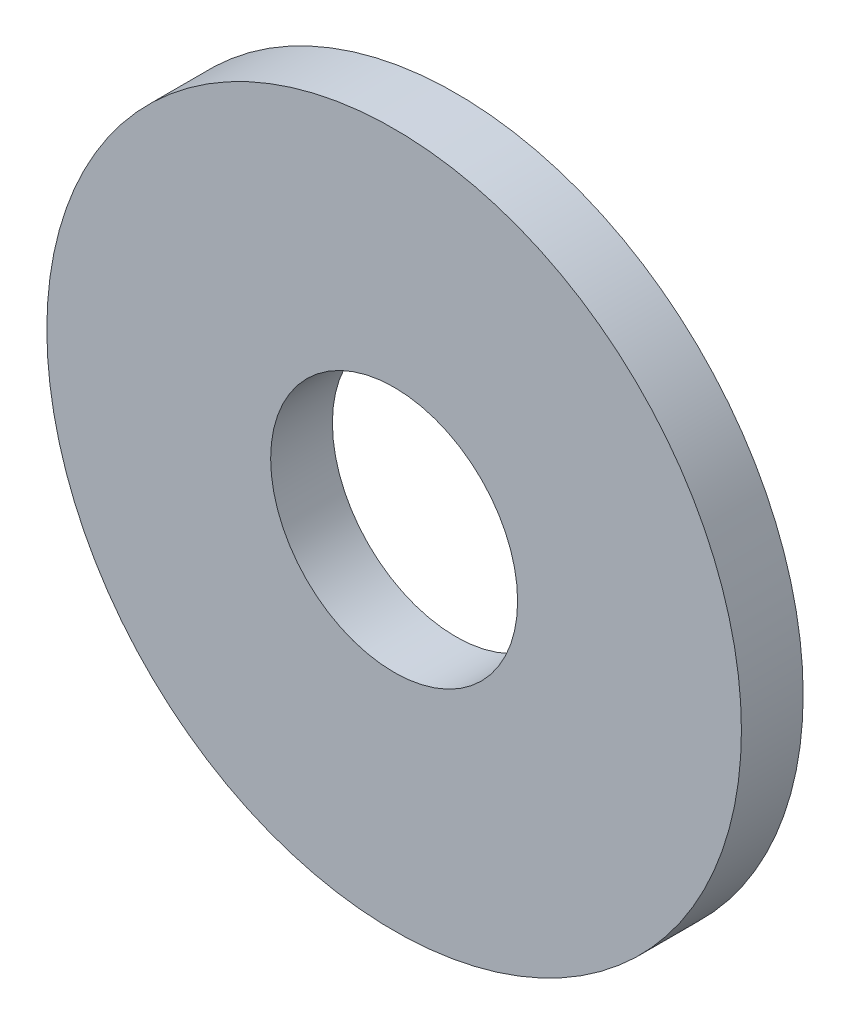
SolidWorks part; units mm, degrees
ref_plane "Front Plane" through (0, 0, 0) normal (0, 0, 1) x (1, 0, 0)
ref_plane "Top Plane" through (0, 0, 0) normal (0, 1, 0) x (1, 0, 0)
ref_plane "Right Plane" through (0, 0, 0) normal (1, 0, 0) x (0, 0, -1)
sketch "Sketch1" plane through (0, 0, 0) normal (1, 0, 0) x (0, 0, -1)
  line L0 (0, -4.5) -> (0, 4.5) construction
  line L1 (0, -1.6) -> (0, 1.6) construction
  line L2 (-0.4, 0) -> (0.4, 0) construction
  point P4 (0, 0)
  point P8 (0, 0)
  point P11 (0, 0)
sketch "Sketch2" plane through (0, 0, 0) normal (0, 0, 1) x (1, 0, 0)
  circle A0 centre (0, 0) radius 4.5
  circle A1 centre (0, 0) radius 1.6
extrude "Boss-Extrude1" add sketch "Sketch2" along normal mid plane 0.8
equation "\"D1@Boss-Extrude1\" = \"Thickness@Sketch1\""
